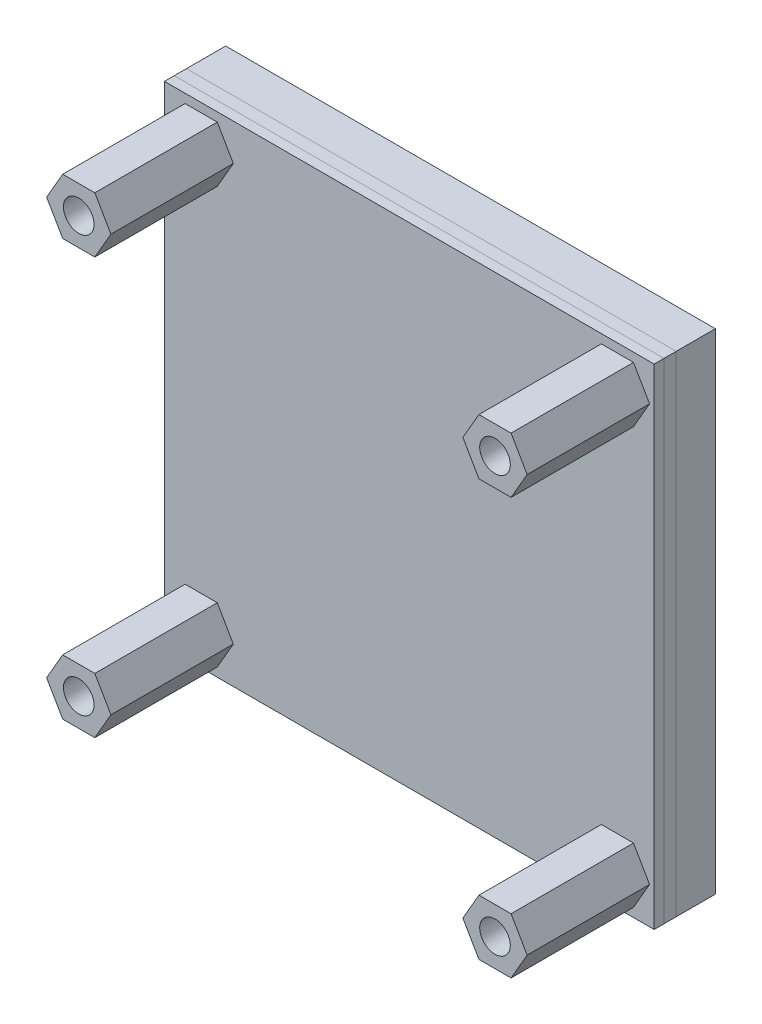
SolidWorks part; units mm, degrees
ref_plane "Front Plane" through (0, 0, 0) normal (0, 0, 1) x (1, 0, 0)
ref_plane "Top Plane" through (0, 0, 0) normal (0, 1, 0) x (1, 0, 0)
ref_plane "Right Plane" through (0, 0, 0) normal (1, 0, 0) x (0, 0, -1)
sketch "Sketch1" plane through (0, 0, 0) normal (0, 0, 1) x (1, 0, 0)
  line L0 (-16.5269, 20.7186) -> (23.4731, 20.7186)
  line L1 (23.4731, 20.7186) -> (23.4731, -19.2814)
  line L2 (23.4731, -19.2814) -> (-16.5269, -19.2814)
  line L3 (-16.5269, -19.2814) -> (-16.5269, 20.7186)
  dimension "D1" = 40
  dimension "D2" = 40
extrude "Boss-Extrude1" add sketch "Sketch1" along normal blind 3.2
sketch "Sketch2" plane through (0, 0, 3.2) normal (0, 0, 1) x (1, 0, 0)
  line L1 (-16.5269, 20.7186) -> (23.4731, 20.7186)
  line L2 (-16.5269, 20.7186) -> (-16.5269, -19.2814)
  line L3 (-16.5269, -19.2814) -> (23.4731, -19.2814)
  line L4 (23.4731, 20.7186) -> (23.4731, -19.2814)
extrude "Boss-Extrude2" add sketch "Sketch2" along normal blind 1 separate body
sketch "Sketch3" plane through (0, 0, 4.2) normal (0, 0, 1) x (1, 0, 0)
  line L1 (-16.5269, 20.7186) -> (23.4731, 20.7186)
  line L2 (-16.5269, 20.7186) -> (-16.5269, -19.2814)
  line L3 (-16.5269, -19.2814) -> (23.4731, -19.2814)
  line L4 (23.4731, 20.7186) -> (23.4731, -19.2814)
extrude "Boss-Extrude3" add sketch "Sketch3" along normal blind 0.8 separate body
sketch "Sketch4" plane through (0, 0, 5) normal (0, 0, 1) x (1, 0, 0)
  line L0 (-13.5269, 27.2207) -> (-13.5269, -29.203) construction
  line L1 (20.4731, 27.2207) -> (20.4731, -29.203) construction
  line L2 (35.9095, 17.7186) -> (-28.3701, 17.7186) construction
  line L3 (-28.3701, -16.2814) -> (34.9929, -16.2814) construction
  line L4 (23.4731, 20.7186) -> (-16.5269, 20.7186) construction
  line L5 (-16.5269, -19.2814) -> (23.4731, -19.2814) construction
  line L7 (23.4731, -19.2814) -> (23.4731, 20.7186) construction
  line L8 (-16.5269, 20.7186) -> (-16.5269, -19.2814) construction
  line L10 (-10.9019, 17.7186) -> (-12.2144, 19.9919)
  line L11 (-12.2144, 19.9919) -> (-14.8394, 19.9919)
  line L12 (-14.8394, 19.9919) -> (-16.1519, 17.7186)
  line L13 (-16.1519, 17.7186) -> (-14.8394, 15.4452)
  line L14 (-14.8394, 15.4452) -> (-12.2144, 15.4452)
  line L15 (-12.2144, 15.4452) -> (-10.9019, 17.7186)
  line L16 (17.8481, 17.7186) -> (19.1606, 15.4452)
  line L17 (19.1606, 15.4452) -> (21.7856, 15.4452)
  line L18 (21.7856, 15.4452) -> (23.0981, 17.7186)
  line L19 (23.0981, 17.7186) -> (21.7856, 19.9919)
  line L20 (21.7856, 19.9919) -> (19.1606, 19.9919)
  line L21 (19.1606, 19.9919) -> (17.8481, 17.7186)
  line L22 (-10.9019, -16.2814) -> (-12.2144, -14.0081)
  line L23 (-12.2144, -14.0081) -> (-14.8394, -14.0081)
  line L24 (-14.8394, -14.0081) -> (-16.1519, -16.2814)
  line L25 (-16.1519, -16.2814) -> (-14.8394, -18.5548)
  line L26 (-14.8394, -18.5548) -> (-12.2144, -18.5548)
  line L27 (-12.2144, -18.5548) -> (-10.9019, -16.2814)
  line L28 (23.0981, -16.2814) -> (21.7856, -14.0081)
  line L29 (21.7856, -14.0081) -> (19.1606, -14.0081)
  line L30 (19.1606, -14.0081) -> (17.8481, -16.2814)
  line L31 (17.8481, -16.2814) -> (19.1606, -18.5548)
  line L32 (19.1606, -18.5548) -> (21.7856, -18.5548)
  line L33 (21.7856, -18.5548) -> (23.0981, -16.2814)
  circle A0 centre (-13.5269, 17.7186) radius 2.625 construction
  circle A1 centre (20.4731, 17.7186) radius 2.625 construction
  circle A2 centre (-13.5269, -16.2814) radius 2.625 construction
  circle A3 centre (20.4731, -16.2814) radius 2.625 construction
  circle A4 centre (20.4731, -16.2814) radius 1.25
  circle A5 centre (-13.5269, -16.2814) radius 1.25
  circle A6 centre (-13.5269, 17.7186) radius 1.25
  circle A7 centre (20.4731, 17.7186) radius 1.25
  dimension "D1" = 3
  dimension "D2" = 3
  dimension "D3" = 3
  dimension "D4" = 3
extrude "Boss-Extrude4" add sketch "Sketch4" along normal blind 10 separate body
